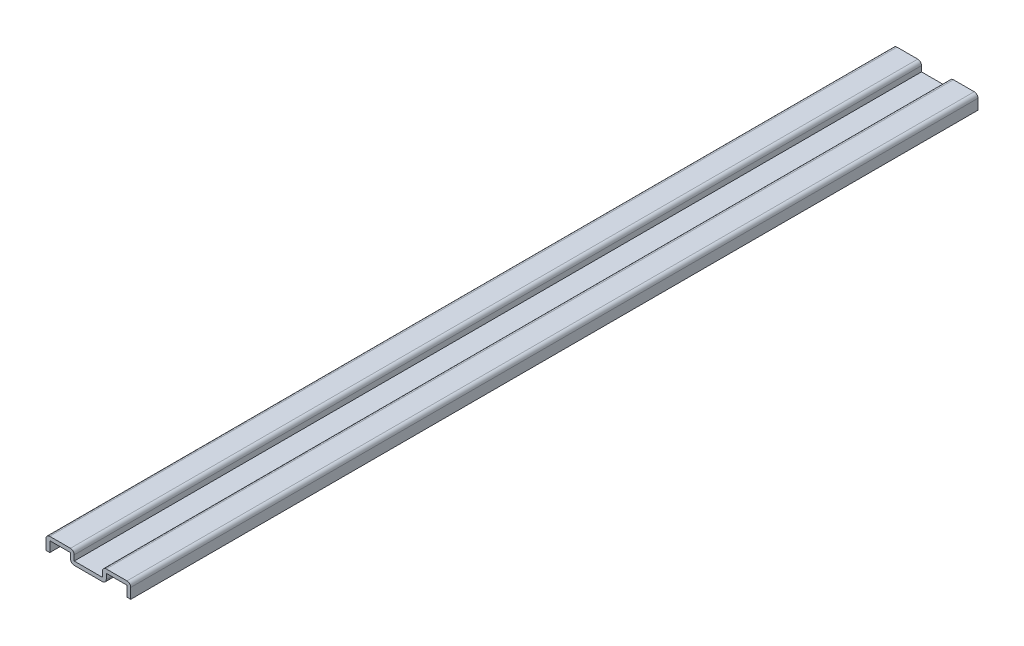
SolidWorks part; units mm, degrees
ref_plane "Front Plane" through (0, 0, 0) normal (0, 0, 1) x (1, 0, 0)
ref_plane "Top Plane" through (0, 0, 0) normal (0, 1, 0) x (1, 0, 0)
ref_plane "Right Plane" through (0, 0, 0) normal (1, 0, 0) x (0, 0, -1)
sketch "Sketch1" plane through (0, 0, 0) normal (0, 0, 1) x (1, 0, 0)
  line L0 (-14.2875, 0) -> (-14.2875, 4.7625)
  line L1 (-14.2875, 4.7625) -> (-4.7625, 4.7625)
  line L2 (-4.7625, 4.7625) -> (-4.7625, 1.6669)
  line L3 (-4.7625, 1.6669) -> (4.7625, 1.6669)
  line L4 (0, 0) -> (0, 7.5965) construction
  line L5 (4.7625, 4.7625) -> (4.7625, 1.6669)
  line L6 (14.2875, 4.7625) -> (4.7625, 4.7625)
  line L7 (14.2875, 0) -> (14.2875, 4.7625)
  point P8 (0, 1.4589)
  point P9 (0, 0)
  point P10 (0, 0)
  point P11 (0, 0)
  point P13 (0, 1.6669)
  dimension "D1" = 28.575
  dimension "D2" = 4.7625
  dimension "D3" = 9.525
  dimension "D4" = 1.6669
extrude "Extrude-Thin1" add sketch "Sketch1" against normal blind 285.75 thin
fillet "Fillet1" radius 1.27 6 edges at (14.2875, 4.7625, -142.875) (4.7625, 4.7625, -142.875) (6.0325, 0.3969, -142.875) (-6.0325, 0.3969, -142.875) (-4.7625, 4.7625, -142.875) (-14.2875, 4.7625, -142.875)
